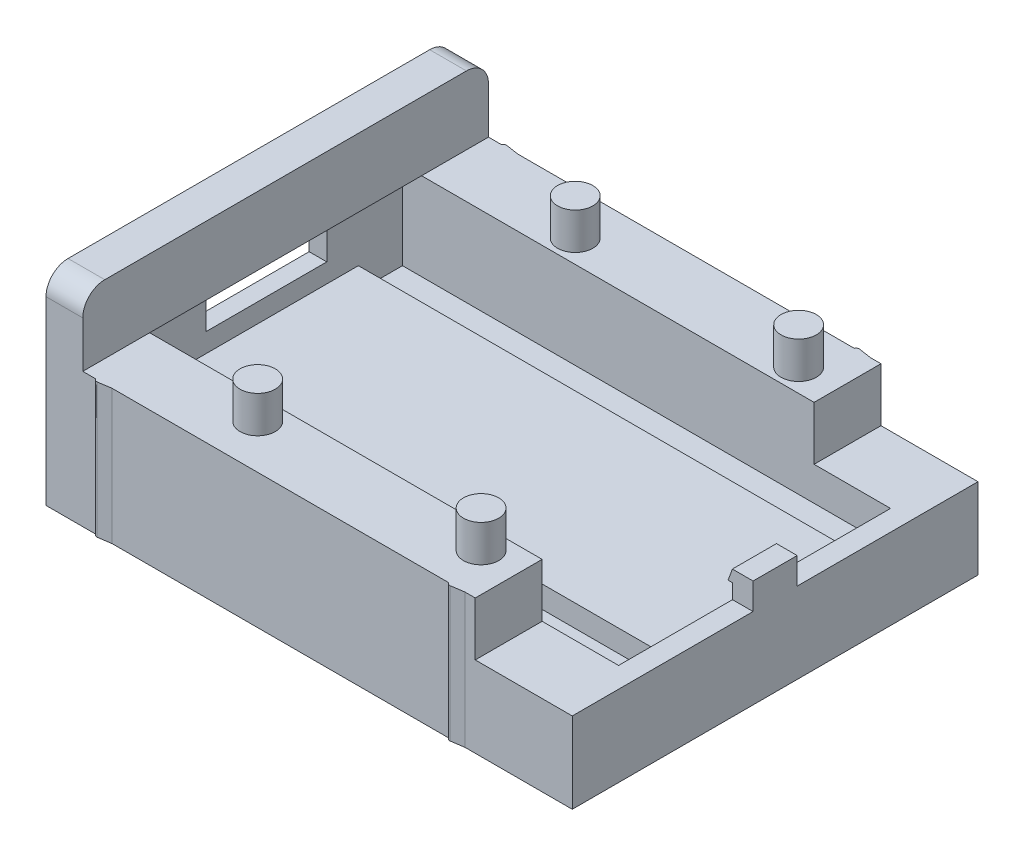
SolidWorks part; units mm, degrees
ref_plane "Ebene vorne" through (0, 0, 0) normal (0, 0, 1) x (1, 0, 0)
ref_plane "Ebene oben" through (0, 0, 0) normal (0, 1, 0) x (1, 0, 0)
ref_plane "Ebene rechts" through (0, 0, 0) normal (1, 0, 0) x (0, 0, -1)
ref_plane "Ebene1" through (0, -4, 0) normal (0, 1, 0) x (1, 0, 0)
sketch "Skizze2" plane through (0, 0, 0) normal (1, 0, 0) x (0, 0, -1)
  line L0 (14, 0) -> (-14, 0)
  line L1 (-14, 0) -> (-14, -4)
  line L6 (14, -4) -> (14, 0)
  line L8 (14, -4) -> (-14, -4)
  dimension "D7" = 4
  dimension "D1" = 28
extrude "Aufsatz-Linear austragen2" add sketch "Skizze2" along normal mid plane 35.8 contours L0 L1 L8 L6
sketch "Skizze4" plane through (0, 0, 0) normal (0, 1, 0) x (1, 0, 0)
  line L0 (17.9, -14) -> (-17.9, -14) construction
  line L1 (17.9, 14) -> (-17.9, 14)
  line L2 (17.9, 14) -> (17.9, -14)
  line L6 (17.9, -14) -> (-17.9, -14)
  line L7 (-17.9, 14) -> (-17.9, -14) construction
  line L8 (-17.9, -14) -> (-17.9, 14)
  line L15 (-16.75, 0) -> (-17.9, 0) construction
  line L16 (17.9, 14) -> (-17.9, 14) construction
  line L17 (17.9, 14) -> (17.9, -14) construction
extrude "Aufsatz-Linear austragen3" add sketch "Skizze4" along normal blind 5
sketch "Skizze7" plane through (-17.9, 0, 0) normal (-1, 0, 0) x (0, 0, 1)
  line L0 (-4.1, 2) -> (4.1, 2)
  line L3 (4.1, 5) -> (-4.1, 5)
  line L6 (0, 5) -> (0, 2) construction
  line L12 (-14, 5) -> (-14, -4) construction
  line L13 (14, 5) -> (14, -4) construction
  line L14 (-4.1, 2) -> (-4.1, 5)
  line L15 (4.1, 2) -> (4.1, 5)
  line L16 (-14, 5) -> (14, 5) construction
  dimension "D3" = 3
  dimension "D4" = 8.2
extrude "Schnitt-Linear austragen4" cut sketch "Skizze7" against normal blind 1.5
sketch "Skizze5" plane through (0, 5, 0) normal (0, 1, 0) x (1, 0, 0)
  line L0 (-16.7, 0) -> (-7.0752, 0) construction
  line L1 (16.5, -9.25) -> (-16.7, -9.25)
  line L2 (16.5, -9.25) -> (16.5, 9.25)
  line L3 (16.5, 9.25) -> (-16.7, 9.25)
  line L4 (-16.7, -9.25) -> (-16.7, 9.25)
  line L5 (-16.75, 0) -> (-17.9, 0) construction
  line L6 (-17.9, -14) -> (-17.9, 14) construction
  dimension "D1" = 33.2
  dimension "D2" = 18.5
  dimension "D3" = 1.2
extrude "Schnitt-Linear austragen2" cut sketch "Skizze5" against normal blind 4.3
sketch "Skizze8" plane through (0, 5, 0) normal (0, 1, 0) x (1, 0, 0)
  line L0 (-17.9, -14) -> (17.9, -14) construction
  line L1 (17.9, 14) -> (-16.7, 14)
  line L2 (17.9, 14) -> (17.9, -14)
  line L3 (17.9, -14) -> (-16.7, -14)
  line L4 (-16.7, 14) -> (-16.7, -14)
extrude "Schnitt-Linear austragen5" cut sketch "Skizze8" against normal blind 3.5
sketch "Skizze10" plane through (0, 0, 0) normal (0, 0, 1) x (1, 0, 0)
  line L0 (17.9, 1.5) -> (16.5, 1.5)
  line L1 (16.5, 1.5) -> (16.5, 2.5)
  line L2 (16.5, 2.5) -> (16.2, 2.5)
  line L3 (16.2, 2.5) -> (16.4912, 3.3)
  line L5 (16.4912, 3.3) -> (17.9, 3.3)
  line L6 (17.9, 3.3) -> (17.9, 1.5)
  dimension "D1" = 1.8
  dimension "D2" = 1
  dimension "D3" = 0.3
  dimension "D4" = 70
extrude "Aufsatz-Linear austragen4" add sketch "Skizze10" along normal mid plane 3
sketch "Skizze9" plane through (0, 0.7, 0) normal (0, 1, 0) x (1, 0, 0)
  line L0 (-16.7, 9.25) -> (-16.7, -9.25) construction
  line L1 (16.5, -9.25) -> (-16.7, -9.25)
  line L2 (16.5, -9.25) -> (16.5, -6.25)
  line L3 (16.5, -6.25) -> (-16.7, -6.25)
  line L4 (-16.7, -9.25) -> (-16.7, -6.25)
  line L5 (16.5, 9.25) -> (-16.7, 9.25)
  line L6 (16.5, 9.25) -> (16.5, 6.25)
  line L7 (16.5, 6.25) -> (-16.7, 6.25)
  line L8 (-16.7, 9.25) -> (-16.7, 6.25)
  line L9 (14.5749, 0) -> (-13.8831, 0) construction
  line L12 (-7.59, 0) -> (7.59, 0) construction
  dimension "D1" = 3
extrude "Schnitt-Linear austragen6" cut sketch "Skizze9" against normal blind 1.5
sketch "Skizze11" plane through (-17.9, 0, 0) normal (-1, 0, 0) x (0, 0, 1)
  line L0 (-14, 5) -> (-14, 9.8)
  line L1 (-14, 9.8) -> (14, 9.8)
  line L2 (-14, 5) -> (14, 5)
  line L3 (0, 0) -> (0, 12.0669) construction
  line L4 (-14, -4) -> (14, -4) construction
  line L5 (14, 5) -> (14, 9.8)
  point P5 (0, 9.8)
  point P18 (0, 5)
  dimension "D1" = 13.8
extrude "Aufsatz-Linear austragen5" add sketch "Skizze11" against normal up to surface (1.2 mm away) up to face at (-16.7, 1.7625, 0)
sketch "Skizze12" plane through (0, 1.5, 0) normal (0, 1, 0) x (1, 0, 0)
  line L0 (16.5, 9.25) -> (-16.7, 9.25) construction
  line L1 (-16.7, 14) -> (11.3, 14)
  line L2 (-16.7, 14) -> (-16.7, 9.25)
  line L3 (-16.7, 9.25) -> (11.3, 9.25)
  line L4 (11.3, 14) -> (11.3, 9.25)
  line L10 (1.238, 0) -> (7.5521, 0) construction
  line L11 (11.3, -14) -> (11.3, -9.25)
  line L12 (-16.7, -9.25) -> (11.3, -9.25)
  line L13 (-16.7, -14) -> (-16.7, -9.25)
  line L14 (-16.7, -14) -> (11.3, -14)
  dimension "D1" = 28
extrude "Aufsatz-Linear austragen6" add sketch "Skizze12" along normal blind 3.65
sketch "Skizze13" plane through (0, 5.15, 0) normal (0, 1, 0) x (1, 0, 0)
  line L0 (-16.7, 14) -> (-16.7, 9.25) construction
  circle A0 centre (-6.5, 10.8) radius 1.2
  dimension "D1" = 2.4
  dimension "D2" = 10.8
  dimension "D3" = 10.2
extrude "Aufsatz-Linear austragen7" add sketch "Skizze13" along normal blind 2.5
pattern_linear "Lineares Muster1" count 2 spacing 15.2 along (1, 0, 0) count 2 spacing 21.6 along (0, 0, 1) of "Aufsatz-Linear austragen7"
sketch "Skizze14" plane through (0, -4, 0) normal (0, -1, 0) x (1, 0, 0)
  line L0 (-17.9, -14) -> (-17.9, -13.8)
  line L2 (-17.9, -13.8) -> (-14.5194, -13.8)
  line L3 (17.9, -14) -> (17.9, 14) construction
  line L4 (17.9, -13.8) -> (17.9, -14)
  line L6 (17.9, -14) -> (-17.9, -14)
  line L10 (0, 0) -> (12.3697, 0) construction
  line L19 (-14.5194, -13.8) -> (-14.4, -13.95)
  line L20 (-14.4, -13.95) -> (-13.4, -13.8)
  line L21 (-13.4, -13.8) -> (9.4806, -13.8)
  line L29 (10.6, -13.8) -> (9.6, -13.95)
  line L30 (9.6, -13.95) -> (9.4806, -13.8)
  line L31 (10.6, -13.8) -> (17.9, -13.8)
  line L32 (10.6, 13.8) -> (17.9, 13.8)
  line L33 (9.6, 13.95) -> (9.4806, 13.8)
  line L34 (10.6, 13.8) -> (9.6, 13.95)
  line L35 (-13.4, 13.8) -> (9.4806, 13.8)
  line L36 (-14.4, 13.95) -> (-13.4, 13.8)
  line L37 (-14.5194, 13.8) -> (-14.4, 13.95)
  line L38 (17.9, 14) -> (-17.9, 14)
  line L39 (17.9, 13.8) -> (17.9, 14)
  line L40 (-17.9, 13.8) -> (-14.5194, 13.8)
  line L41 (-17.9, 14) -> (-17.9, 13.8)
  dimension "D1" = 0.15
  dimension "D2" = 0.2
  dimension "D3" = 3.5
  dimension "D4" = 1
  dimension "D5" = 120
  dimension "D6" = 120
  dimension "D7" = 24
  dimension "D8" = 1
  dimension "D9" = 0.15
extrude "Schnitt-Linear austragen7" cut sketch "Skizze14" against normal through all
fillet "Verrundung1" radius 0.2 4 edges at (-14.4, 0.575, -13.95) (9.6, 0.575, 13.95) (-14.4, 0.575, 13.95) (9.6, 0.575, -13.95)
sketch "Skizze20" plane through (-16.7, 0, 0) normal (1, 0, 0) x (0, 0, -1)
  line L0 (-9.25, 5.15) -> (-13.8, 5.15) construction
  line L1 (-13.8, 9.8) -> (-13.8, 5.15) construction
  line L2 (13.8, 9.8) -> (-13.8, 9.8) construction
  line L3 (13.8, 5.15) -> (13.8, 9.8) construction
  line L4 (13.8, 5.15) -> (-13.8, 5.15)
  line L5 (-13.8, 9.8) -> (-13.8, 5.15)
  line L6 (13.8, 9.8) -> (-13.8, 9.8)
  line L7 (13.8, 5.15) -> (13.8, 9.8)
extrude "Aufsatz-Linear austragen8" add sketch "Skizze20" along normal blind 1.3
fillet "Verrundung2" radius 1.5 2 edges at (-16.65, 9.8, 13.8) (-16.65, 9.8, -13.8)
sketch "Skizze21" plane through (-17.9, 0, 0) normal (-1, 0, 0) x (0, 0, 1)
  line L0 (-14, -3.5) -> (-10.5, -3.5) construction
  line L2 (15.3286, 0) -> (-15.3286, 0) construction
  line L3 (0, -7.59) -> (0, 7.59) construction
  text T0 "L" font "Arial" height in points 14
  point P5 (-9.7142, -1.8787)
  point P8 (-12, -3)
  dimension "D1" = 14
  dimension "D2" = 3.5
  dimension "D3" = 3.5
extrude "Schnitt-Linear austragen8" cut sketch "Skizze21" against normal blind 1
